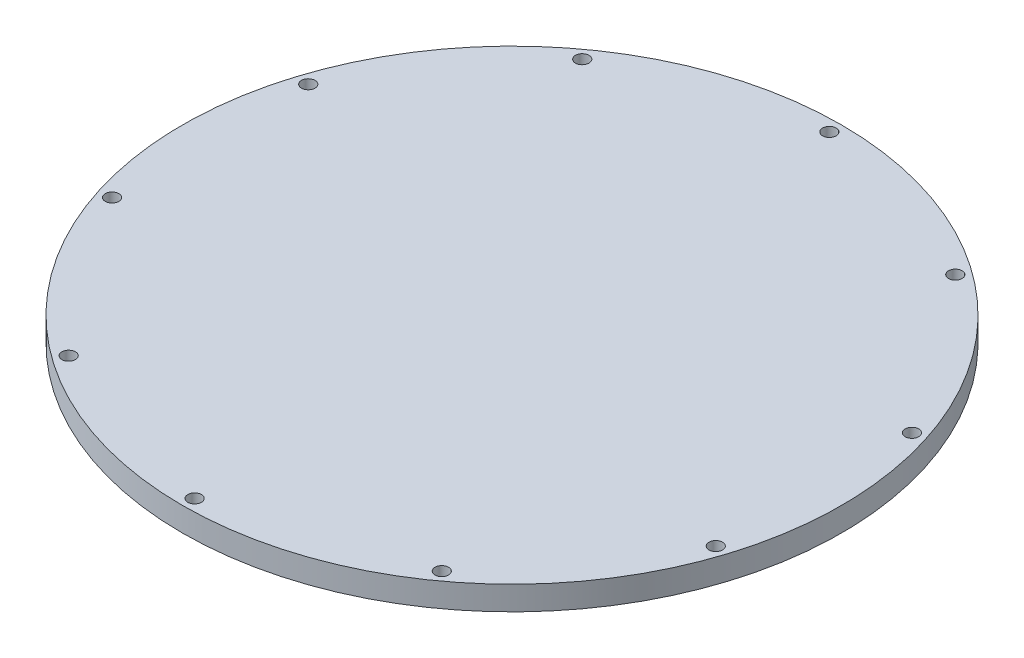
SolidWorks part; units mm, degrees
material "Acrylic (Medium-high impact)"
ref_plane "Front Plane" through (0, 0, 0) normal (0, 0, 1) x (1, 0, 0)
ref_plane "Top Plane" through (0, 0, 0) normal (0, 1, 0) x (1, 0, 0)
ref_plane "Right Plane" through (0, 0, 0) normal (1, 0, 0) x (0, 0, -1)
sketch "Sketch1" plane through (0, 0, 0) normal (0, 1, 0) x (1, 0, 0)
  line L0 (0, 0) -> (0, 79.5) construction
  line L1 (0, 0) -> (46.7289, 64.3169) construction
  circle A0 centre (0, 0) radius 79.5 construction
  circle A1 centre (0, 0) radius 82.55
  point P4 (0, 79.5)
  point P5 (46.7289, 64.3169)
  point P8 (75.609, 24.5669)
  point P9 (75.609, -24.5669)
  point P10 (46.7289, -64.3169)
  point P11 (0, -79.5)
  point P12 (-46.7289, -64.3169)
  point P13 (-75.609, -24.5669)
  point P14 (-75.609, 24.5669)
  point P15 (-46.7289, 64.3169)
  point P16 (0, 0)
  dimension "D1" = 159
  dimension "D2" = 165.1
  dimension "D4" = 36
  dimension "D3" = 10
extrude "Boss-Extrude1" add sketch "Sketch1" along normal mid plane 6
hole_wizard "M3 Clearance Hole1" positions "Sketch2" profile "Sketch3" hole size "M3" standard "ANSI Metric" end condition through all
sketch "Sketch2" plane through (0, 3, 0) normal (0, 1, 0) x (1, 0, 0)
  point P0 (0, 79.5)
  point P3 (46.7289, 64.3169)
  point P6 (75.609, 24.5669)
  point P9 (75.609, -24.5669)
  point P12 (46.7289, -64.3169)
  point P15 (0, -79.5)
  point P18 (-46.7289, -64.3169)
  point P21 (-75.609, -24.5669)
  point P24 (-75.609, 24.5669)
  point P27 (-46.7289, 64.3169)
sketch "Sketch3" plane through (0, 3, -79.5) normal (1, 0, 0) x (0, 0, 1)
  line L0 (0, 0) -> (0, 6)
  line L1 (0, 6) -> (1.7, 6)
  line L2 (1.7, 6) -> (1.7, 0)
  line L5 (1.7, 0) -> (0, 0)
  line L11 (0, -6.35) -> (0, 107.95) construction
  dimension "Thru Hole Dia." = 3.4
  dimension "Thru Hole Depth" = 6
